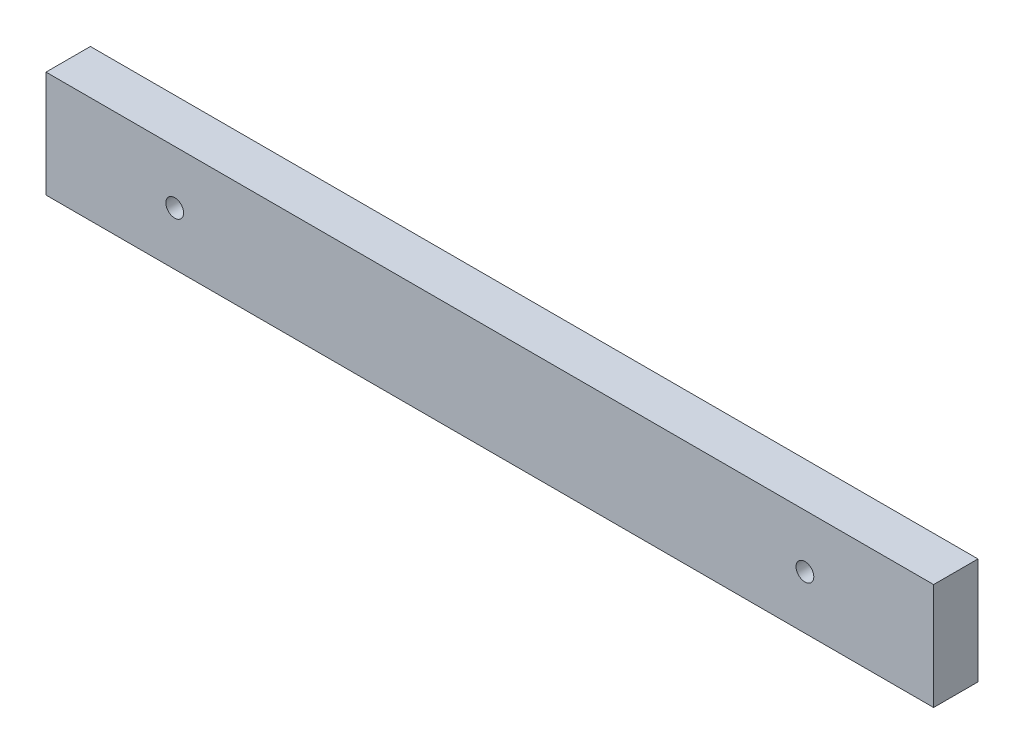
SolidWorks part; units mm, degrees
ref_plane "Front Plane" through (0, 0, 0) normal (0, 0, 1) x (1, 0, 0)
ref_plane "Top Plane" through (0, 0, 0) normal (0, 1, 0) x (1, 0, 0)
ref_plane "Right Plane" through (0, 0, 0) normal (1, 0, 0) x (0, 0, -1)
sketch "Sketch1" plane through (0, 0, 0) normal (0, 0, 1) x (1, 0, 0)
  line L1 (0, 0) -> (100, 0)
  line L2 (0, 0) -> (0, 12)
  line L3 (0, 12) -> (100, 12)
  line L4 (100, 0) -> (100, 12)
  dimension "D1" = 12
  dimension "D2" = 100
extrude "Boss-Extrude1" add sketch "Sketch1" along normal blind 5
sketch "Sketch2" plane through (0, 0, 5) normal (0, 0, 1) x (1, 0, 0)
  line L0 (0, 0) -> (100, 0) construction
  line L1 (50, 12) -> (50, 0) construction
  line L2 (100, 12) -> (0, 12) construction
  circle A0 centre (14.5, 6) radius 1
  circle A1 centre (85.5, 6) radius 1
  point P10 (0, 0)
  point P11 (0, 0)
  dimension "D1" = 2
  dimension "D2" = 2
  dimension "D3" = 71
  dimension "D4" = 6
extrude "Cut-Extrude1" cut sketch "Sketch2" against normal through all
